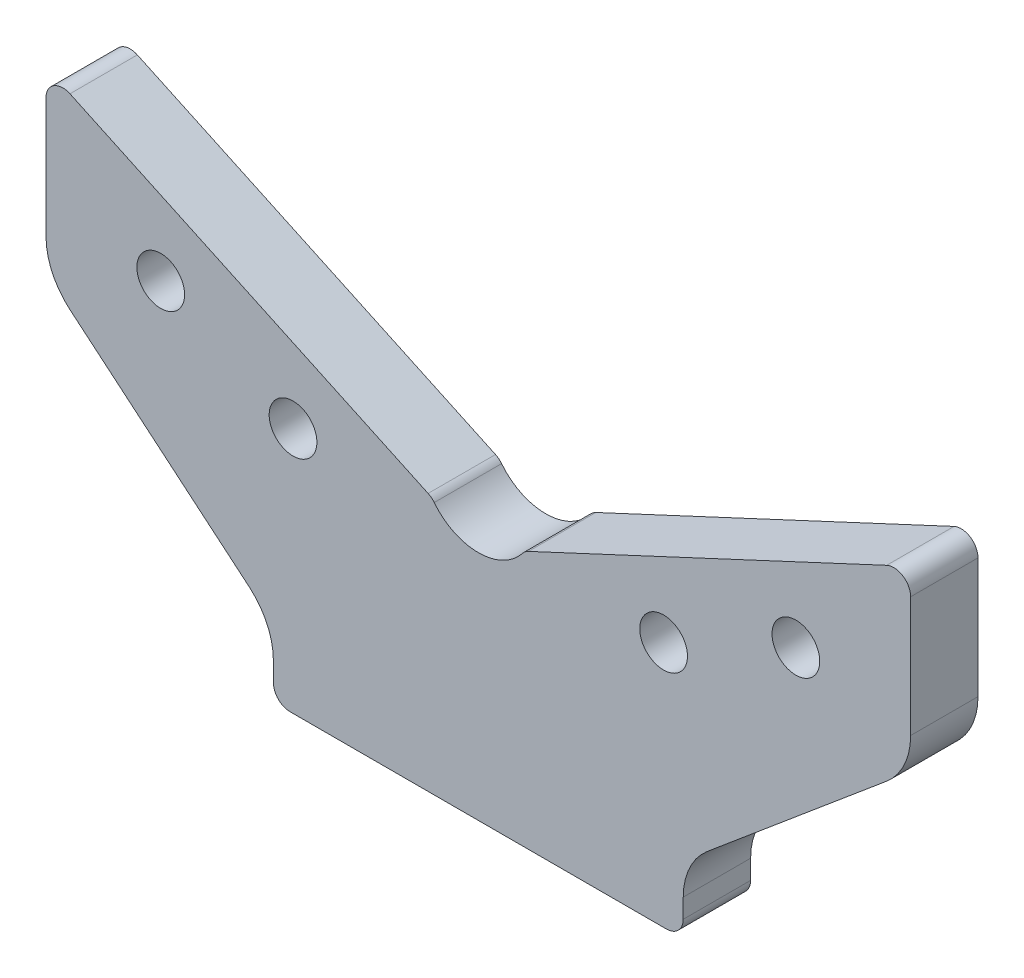
SolidWorks part; units mm, degrees
ref_plane "Front" through (0, 0, 0) normal (0, 0, 1) x (1, 0, 0)
ref_plane "Top" through (0, 0, 0) normal (0, 1, 0) x (1, 0, 0)
ref_plane "Right" through (0, 0, 0) normal (1, 0, 0) x (0, 0, -1)
sketch "Sketch1" plane through (0, 0, 0) normal (0, 0, 1) x (1, 0, 0)
  line L0 (36.5, 6.4208) -> (36.5, 3)
  line L1 (-36.5, 6.4208) -> (-36.5, 3)
  line L2 (0, 0) -> (33.5, 0)
  line L3 (0, 0) -> (-33.5, 0)
  line L4 (72.7321, 75.7189) -> (8.9396, 45.972)
  line L5 (0, 0) -> (0, 41.8034) construction
  line L6 (-77, 51.5957) -> (-77, 73)
  line L7 (-72.7321, 75.7189) -> (-8.9396, 45.972)
  line L8 (40.7865, 15.6133) -> (72.7135, 42.4032)
  line L10 (77, 51.5957) -> (77, 73)
  line L11 (-40.7865, 15.6133) -> (-72.7135, 42.4032)
  arc A0 (40.7865, 15.6133) -> (36.5, 6.4208) centre (48.5, 6.4208) ccw
  arc A1 (-40.7865, 15.6133) -> (-36.5, 6.4208) centre (-48.5, 6.4208) cw
  arc A2 (36.5, 3) -> (33.5, 0) centre (33.5, 3) cw
  arc A3 (72.7321, 75.7189) -> (77, 73) centre (74, 73) cw
  arc A4 (-77, 73) -> (-72.7321, 75.7189) centre (-74, 73) cw
  arc A5 (72.7135, 42.4032) -> (77, 51.5957) centre (65, 51.5957) ccw
  arc A6 (-36.5, 3) -> (-33.5, 0) centre (-33.5, 3) ccw
  arc A9 (-72.7135, 42.4032) -> (-77, 51.5957) centre (-65, 51.5957) cw
  arc A10 (-7.8519, 45.1108) -> (7.8519, 45.1108) centre (0, 51.3034) ccw
  arc A11 (-7.8519, 45.1108) -> (-8.9396, 45.972) centre (-10.2075, 43.2531) ccw
  arc A12 (7.8519, 45.1108) -> (8.9396, 45.972) centre (10.2075, 43.2531) cw
  point P14 (36.5, 0)
  point P19 (77, 77.7091)
  point P23 (-77, 77.7091)
  point P24 (-36.5, 0)
  point P26 (77, 0)
  point P32 (77, 46)
  point P43 (0, 41.8034)
  dimension "D5" = 30
  dimension "D6" = 3
  dimension "D7" = 73
  dimension "D8" = 3
  dimension "D13" = 12
  dimension "D15" = 10
  dimension "D16" = 3
  dimension "D2" = 12
  dimension "D3" = 65
  dimension "D4" = 25
  dimension "D9" = 154
  dimension "D10" = 76
  dimension "D11" = 50
  dimension "D14" = 9.5
extrude "Extrude1" add sketch "Sketch1" along normal blind 12
hole_wizard "M10 gevindhuller" positions "Sketch5" profile "Sketch4" legacy
sketch "Sketch5" plane through (0, 0, 12) normal (0, 0, 1) x (1, 0, 0)
  line L0 (0, 0) -> (0, 51.3034) construction
  line L1 (72.7321, 75.7189) -> (8.9396, 45.972) construction
  line L2 (56.564, 54.9391) -> (33, 43.951) construction
  point P6 (-33, 43.951)
  point P8 (-56.564, 54.9391)
  point P9 (56.564, 54.9391)
  point P11 (33, 43.951)
  dimension "D1" = 66
  dimension "D2" = 12
  dimension "D3" = 26
sketch "Sketch4" plane through (-33, 43.951, 12) normal (1, 0, 0) x (0, -1, 0)
  line L0 (0, 0) -> (0, 24.5537)
  line L1 (0, 24.5537) -> (4.25, 22)
  line L2 (4.25, 22) -> (4.25, 0)
  line L4 (4.25, 0) -> (0, 0)
  line L6 (0, 24.5537) -> (-4.25, 22) construction
  line L7 (0, -4.2442) -> (0, 117.3081) construction
  dimension "Diameter" = 8.5
  dimension "Depth" = 22
  dimension "Drill Angle" = 118
cosmetic thread "Cosmetic Thread2" parameters "D1"=17, "D2"=10
cosmetic thread "Cosmetic Thread3" parameters "D1"=17, "D2"=10
cosmetic thread "Cosmetic Thread4" parameters "D1"=8, "D2"=10
cosmetic thread "Cosmetic Thread5" parameters "D1"=8, "D2"=10
